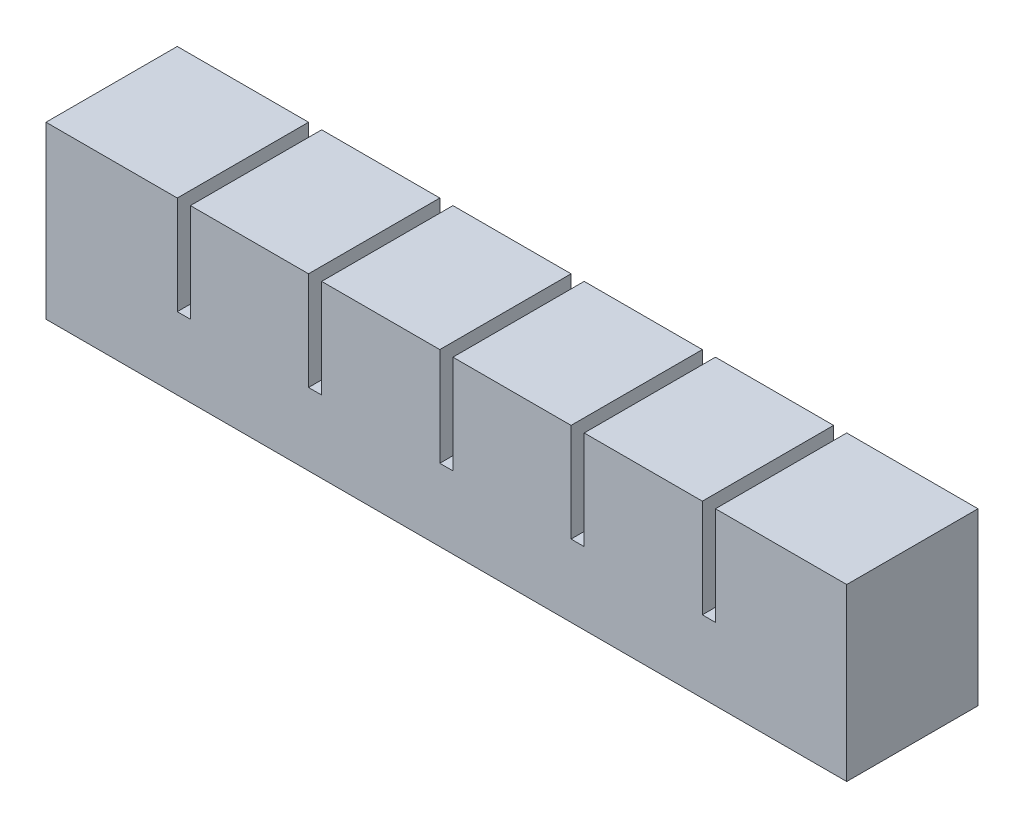
SolidWorks part; units mm, degrees
ref_plane "Front Plane" through (0, 0, 0) normal (0, 0, 1) x (1, 0, 0)
ref_plane "Top Plane" through (0, 0, 0) normal (0, 1, 0) x (1, 0, 0)
ref_plane "Right Plane" through (0, 0, 0) normal (1, 0, 0) x (0, 0, -1)
sketch "Sketch1" plane through (0, 0, 0) normal (0, 0, 1) x (1, 0, 0)
  line L1 (0, 0) -> (18, 0)
  line L2 (0, 0) -> (0, 20)
  line L3 (0, 20) -> (18, 20)
  line L4 (18, 0) -> (18, 20)
  dimension "D1" = 18
  dimension "D2" = 20
extrude "Boss-Extrude1" add sketch "Sketch1" along normal blind 20
sketch "Sketch2" plane through (0, 0, 0) normal (0, -1, 0) x (1, 0, 0)
  line L0 (18, 20) -> (18, 0) construction
  line L1 (4, 16) -> (14, 16)
  line L2 (4, 16) -> (4, 4)
  line L3 (4, 4) -> (14, 4)
  line L4 (14, 16) -> (14, 4)
  line L5 (0, 20) -> (18, 20) construction
  line L6 (0, 20) -> (0, 0) construction
  line L7 (0, 0) -> (18, 0) construction
  dimension "D1" = 4
  dimension "D2" = 4
  dimension "D3" = 4
  dimension "D4" = 4
extrude "Cut-Extrude1" cut sketch "Sketch2" against normal blind 16
sketch "Sketch3" plane through (18, 0, 0) normal (1, 0, 0) x (0, 0, -1)
  line L0 (0, 0) -> (0, 20) construction
  line L1 (-20, 0) -> (0, 0)
  line L2 (-20, 0) -> (-20, 5)
  line L3 (-20, 5) -> (0, 5)
  line L4 (0, 0) -> (0, 5)
  dimension "D1" = 5
extrude "Boss-Extrude2" add sketch "Sketch3" along normal blind 2
pattern_linear "LPattern1" count 6 spacing 20 along (1, 0, 0) of bodies 103
sketch "Sketch4" plane through (118, 0, 0) normal (1, 0, 0) x (0, 0, -1)
  line L1 (-20, 20) -> (0, 20)
  line L2 (-20, 20) -> (-20, 5)
  line L3 (-20, 5) -> (0, 5)
  line L4 (0, 20) -> (0, 5)
extrude "Boss-Extrude3" add sketch "Sketch4" along normal up to surface (2 mm away) up to face at (120, 2.5, 10)
sketch "Sketch5" plane through (0, 0, 0) normal (-1, 0, 0) x (0, 0, 1)
  line L1 (0, 20) -> (20, 20)
  line L2 (0, 20) -> (0, 0)
  line L3 (0, 0) -> (20, 0)
  line L4 (20, 20) -> (20, 0)
extrude "Boss-Extrude4" add sketch "Sketch5" along normal blind 2
combine bodies "Combine1" operation type add bodies to combine 104 105 106 107 110 109
ref_point "Point1"
sketch "Sketch6" plane through (0, 0, 0) normal (0, -1, 0) x (1, 0, 0)
  line L0 (114, 4) -> (114, 16) construction
  line L1 (4, 9) -> (114, 9)
  line L2 (4, 9) -> (4, 11)
  line L3 (4, 11) -> (114, 11)
  line L4 (114, 9) -> (114, 11)
  line L5 (4, 9) -> (114, 11) construction
  line L6 (4, 11) -> (114, 9) construction
  point P0 (59, 10)
  dimension "D1" = 2
extrude "Cut-Extrude2" cut sketch "Sketch6" against normal blind 2
sketch "Sketch7" plane through (0, 0, 0) normal (0, -1, 0) x (1, 0, 0)
  line L1 (-2, 20) -> (120, 20)
  line L2 (-2, 20) -> (-2, 0)
  line L3 (-2, 0) -> (120, 0)
  line L4 (120, 20) -> (120, 0)
extrude "Boss-Extrude5" add sketch "Sketch7" along normal blind 6
